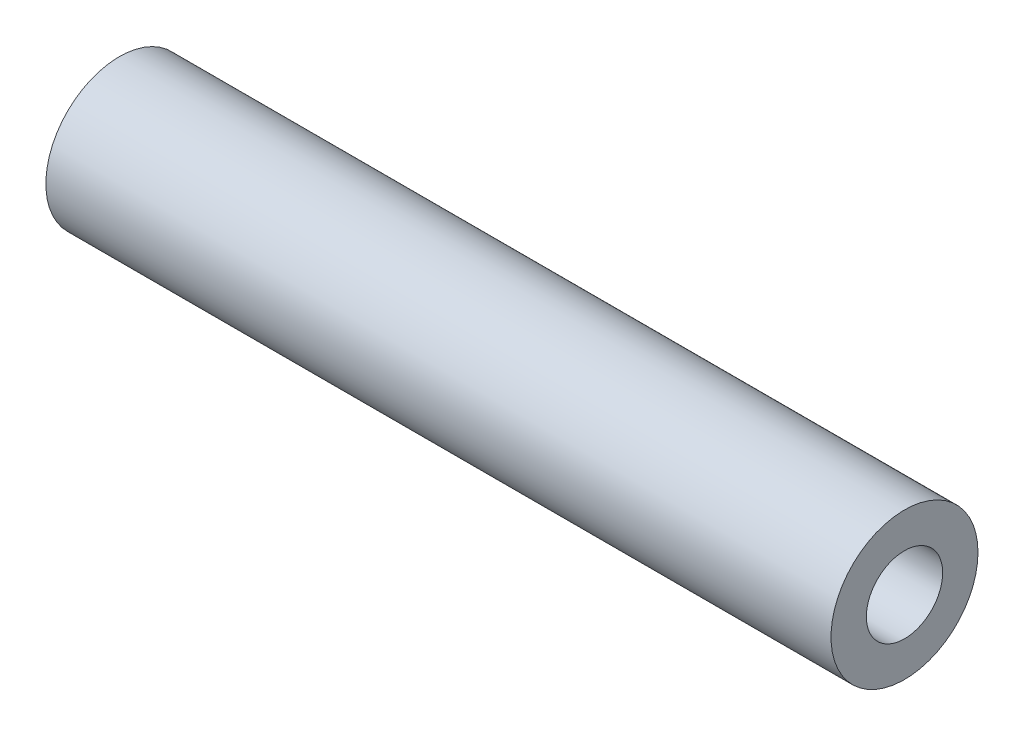
SolidWorks part; units mm, degrees
material "Custom Plastic"
ref_plane "Front Plane" through (0, 0, 0) normal (0, 0, 1) x (1, 0, 0)
ref_plane "Top Plane" through (0, 0, 0) normal (0, 1, 0) x (1, 0, 0)
ref_plane "Right Plane" through (0, 0, 0) normal (1, 0, 0) x (0, 0, -1)
sketch "Sketch1" plane through (0, 0, 0) normal (1, 0, 0) x (0, 0, -1)
  circle A0 centre (0, 0) radius 42.799
  circle A1 centre (0, 0) radius 22.225
  dimension "D1" = 85.598
  dimension "D2" = 44.45
extrude "Boss-Extrude1" add sketch "Sketch1" along normal blind 457.2
